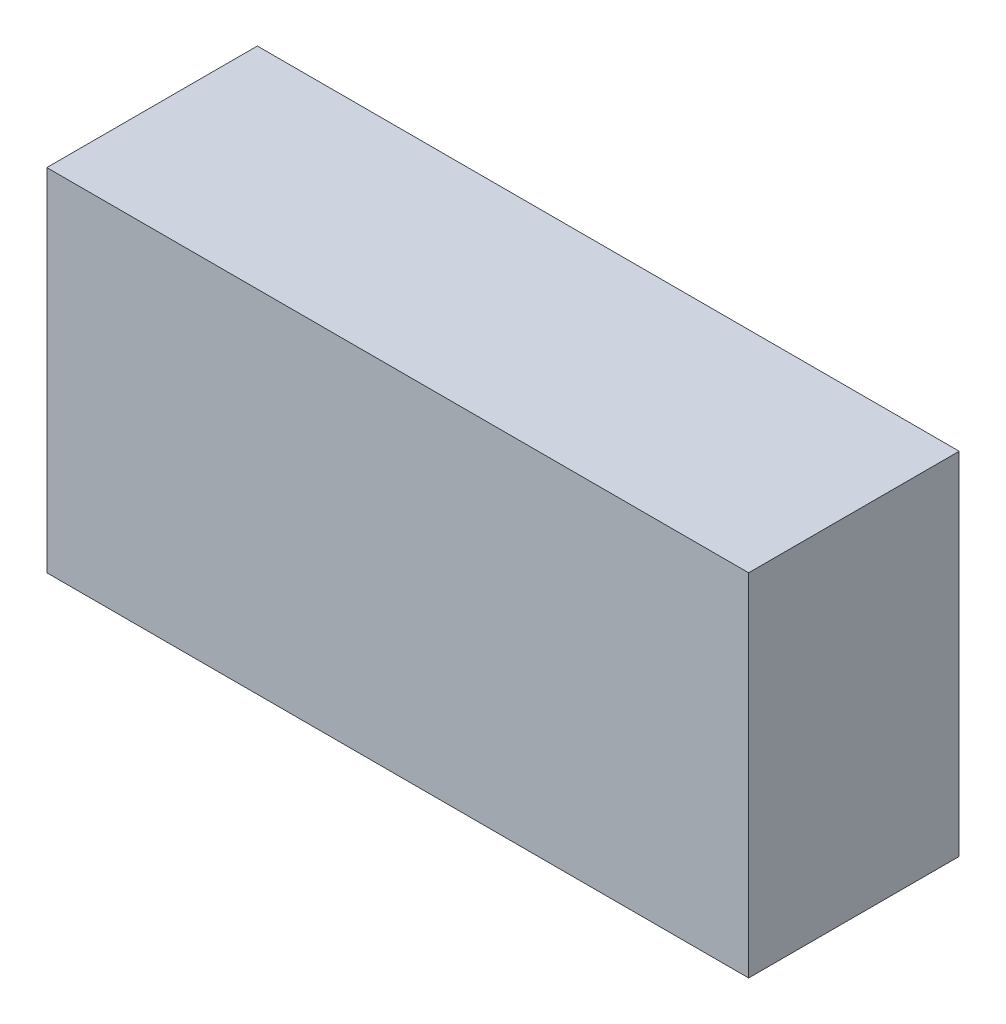
SolidWorks part; units mm, degrees
ref_plane "Plano frontal" through (0, 0, 0) normal (0, 0, 1) x (1, 0, 0)
ref_plane "Plano superior" through (0, 0, 0) normal (0, 1, 0) x (1, 0, 0)
ref_plane "Plano direito" through (0, 0, 0) normal (1, 0, 0) x (0, 0, -1)
sketch "Esboço1" plane through (0, 0, 0) normal (0, 0, 1) x (1, 0, 0)
  line L1 (5, -2.5) -> (-5, -2.5)
  line L2 (5, -2.5) -> (5, 2.5)
  line L3 (5, 2.5) -> (-5, 2.5)
  line L4 (-5, -2.5) -> (-5, 2.5)
  line L5 (5, -2.5) -> (-5, 2.5) construction
  line L6 (5, 2.5) -> (-5, -2.5) construction
  point P0 (0, 0)
  dimension "D1" = 10
  dimension "D2" = 5
extrude "Ressalto-extrusão1" add sketch "Esboço1" along normal blind 3
